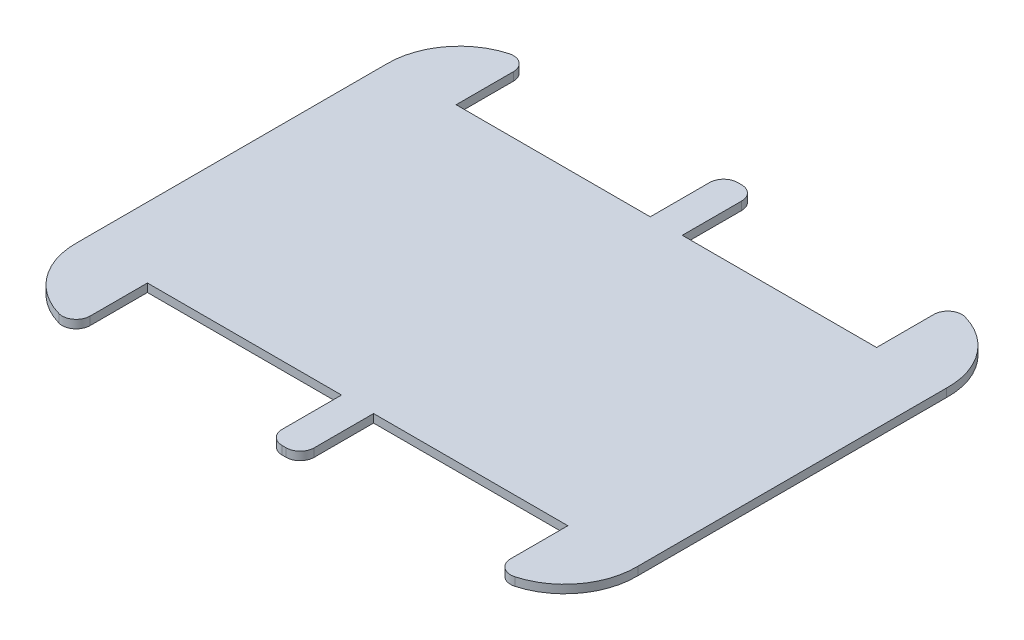
SolidWorks part; units mm, degrees
ref_plane "Front Plane" through (0, 0, 0) normal (0, 0, 1) x (1, 0, 0)
ref_plane "Top Plane" through (0, 0, 0) normal (0, 1, 0) x (1, 0, 0)
ref_plane "Right Plane" through (0, 0, 0) normal (1, 0, 0) x (0, 0, -1)
sketch "Sketch1" plane through (0, 0, 0) normal (0, 1, 0) x (1, 0, 0)
  line L0 (0, -82.55) -> (0, 82.55) construction
  line L1 (-101.6, 82.55) -> (101.6, 82.55) construction
  line L2 (-101.6, 82.55) -> (-101.6, -82.55) construction
  line L3 (-101.6, -82.55) -> (101.6, -82.55) construction
  line L4 (101.6, 82.55) -> (101.6, -82.55) construction
  line L5 (-101.6, 82.55) -> (101.6, -82.55) construction
  line L6 (-101.6, -82.55) -> (101.6, 82.55) construction
  line L7 (-101.6, 55.95) -> (101.6, 55.95) construction
  line L8 (101.6, -55.95) -> (-101.6, -55.95) construction
  line L9 (76.2, 82.55) -> (76.2, -82.55) construction
  line L10 (-76.2, 82.55) -> (-76.2, -82.55) construction
  line L11 (-76.2, 82.55) -> (-76.2, 55.95)
  line L12 (-76.2, 55.95) -> (-5.842, 55.95)
  line L13 (-5.842, -55.95) -> (-5.842, -82.55) construction
  line L14 (-5.842, -82.55) -> (5.7702, -82.55) construction
  line L15 (76.2, 55.95) -> (5.7702, 55.9499)
  line L16 (5.7702, -82.55) -> (5.7702, -55.95) construction
  line L17 (-76.2, -82.55) -> (-76.2, -55.95)
  line L18 (-76.2, -55.95) -> (-5.842, -55.95)
  line L19 (-5.842, -55.95) -> (-5.842, -82.55)
  line L20 (-5.842, -82.55) -> (5.7702, -82.55)
  line L21 (5.7702, -82.55) -> (5.7702, -55.95)
  line L22 (-5.842, -55.95) -> (-5.842, 82.55) construction
  line L23 (76.2, -55.95) -> (76.2, -82.55)
  line L24 (76.2, 82.55) -> (76.2, 55.95)
  line L25 (5.7702, -55.95) -> (76.2, -55.95)
  line L26 (5.7702, -55.95) -> (5.7702, 82.55) construction
  line L27 (5.7702, 55.9499) -> (5.7702, 82.55)
  line L28 (5.7702, 82.55) -> (-5.842, 82.55)
  line L29 (-5.842, 82.55) -> (-5.842, 55.95)
  line L30 (101.6, -55.95) -> (101.6, 55.95)
  line L31 (-101.6, -55.95) -> (-101.6, 55.95)
  arc A0 (76.2, -82.55) -> (101.6, -55.95) centre (75.6, -56.55) ccw
  arc A1 (-76.2, -82.55) -> (-101.6, -55.95) centre (-75.6, -56.55) cw
  arc A2 (76.2, 82.55) -> (101.6, 55.95) centre (75.6, 56.55) cw
  arc A3 (-76.2, 82.55) -> (-101.6, 55.95) centre (-75.6, 56.55) ccw
  point P0 (0, 0)
  dimension "D1" = 165.1
  dimension "D2" = 203.2
  dimension "D3" = 26.6
  dimension "D4" = 26.6
  dimension "D5" = 25.4
  dimension "D6" = 25.4
  dimension "D7" = 11.6122
  dimension "D8" = 5.842
extrude "Boss-Extrude1" add sketch "Sketch1" along normal blind 3
fillet "Fillet1" radius 5.08 2 edges at (-5.842, 1.5, 82.55) (5.7702, 1.5, 82.55)
fillet "Fillet2" radius 5.08 2 edges at (-5.842, 1.5, -82.55) (5.7702, 1.5, -82.55)
fillet "Fillet3" radius 5.08 4 edges at (76.2, 1.5, -82.55) (-76.2, 1.5, -82.55) (-76.2, 1.5, 82.55) (76.2, 1.5, 82.55)
